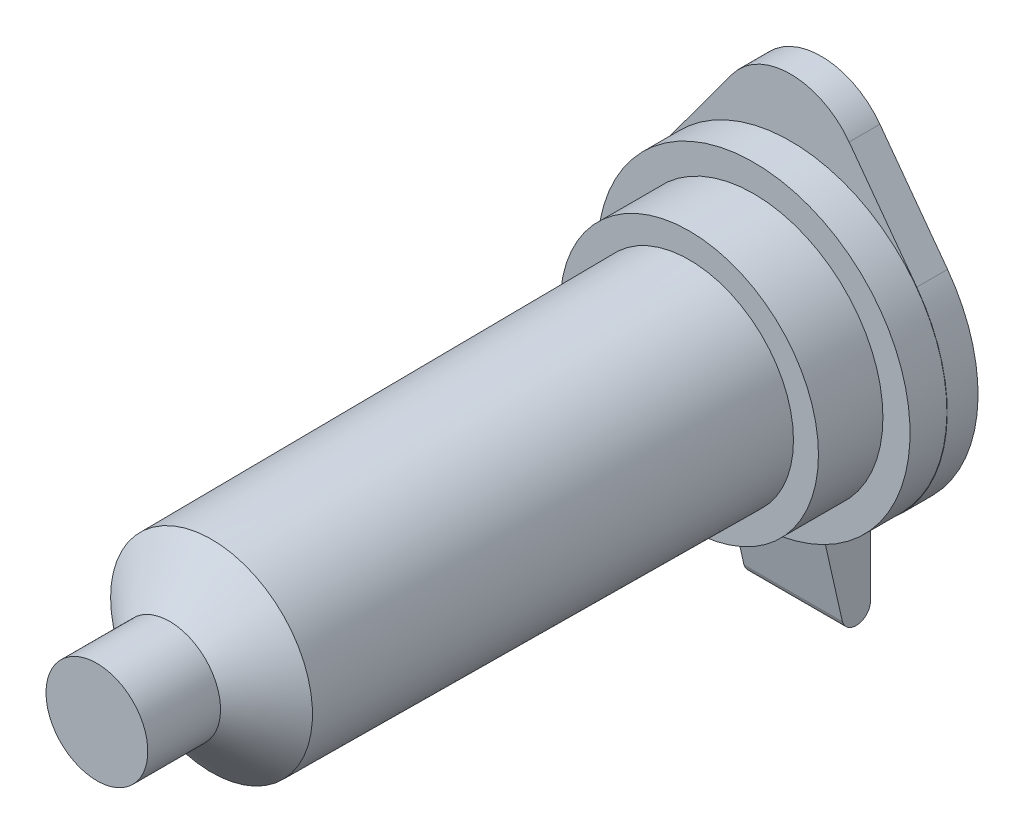
SolidWorks part; units mm, degrees
ref_plane "Front Plane" through (0, 0, 0) normal (0, 0, 1) x (1, 0, 0)
ref_plane "Top Plane" through (0, 0, 0) normal (0, 1, 0) x (1, 0, 0)
ref_plane "Right Plane" through (0, 0, 0) normal (1, 0, 0) x (0, 0, -1)
sketch "Sketch1" plane through (0, 0, 0) normal (0, 1, 0) x (1, 0, 0)
  line L1 (0, 0) -> (2.1, 0)
  line L2 (2.1, 0) -> (2.1, 3)
  line L3 (2.1, 3) -> (4.165, 4.73)
  line L4 (4.165, 4.73) -> (4.3, 24.44)
  line L5 (4.3, 24.44) -> (5.33, 24.44)
  line L6 (5.33, 24.44) -> (5.33, 27.1)
  line L7 (5.33, 27.1) -> (6.45, 27.1)
  line L8 (6.45, 27.1) -> (6.45, 28.62)
  line L9 (6.45, 28.62) -> (0, 28.62)
  line L10 (0, 28.62) -> (0, 0)
  dimension "D1" = 2.1
  dimension "D2" = 3
  dimension "D3" = 4.165
  dimension "D4" = 4.3
  dimension "D5" = 5.33
  dimension "D6" = 6.45
  dimension "D7" = 28.62
  dimension "D8" = 1.52
  dimension "D9" = 4.18
  dimension "D10" = 4.73
revolve "Revolve1" add sketch "Sketch1" angle 360 about L10
sketch "Sketch2" plane through (0, 0, -28.62) normal (0, 0, -1) x (-1, 0, 0)
  line L0 (5.2065, 3.8325) -> (2.416, 7.6234)
  line L1 (-2.416, 7.6234) -> (-5.2065, 3.8325)
  arc A0 (-5.2065, 3.8325) -> (5.2065, 3.8325) centre (0, 0) ccw
  arc A1 (2.416, 7.6234) -> (-2.416, 7.6234) centre (0, 5.845) ccw
  point P5 (0, 8.845)
  point P6 (0, -6.465)
  dimension "D1" = 12.93
  dimension "D3" = 6
  dimension "D2" = 15.31
extrude "Boss-Extrude1" add sketch "Sketch2" along normal blind 1.27
sketch "Sketch3" plane through (0, 0, 0) normal (1, 0, 0) x (0, 0, -1)
  line L0 (29.89, -5.6679) -> (29.89, -9.5931)
  line L1 (29.89, -6.465) -> (29.89, 3.8325) construction
  line L2 (28.7295, -9.7689) -> (27.8039, -5.6679)
  line L3 (27.8039, -5.6679) -> (29.89, -5.6679)
  line L5 (24.44, -5.33) -> (27.1, -5.33) construction
  arc A0 (29.89, -9.5931) -> (28.7295, -9.7689) centre (29.2964, -9.5931) cw
  point P9 (29.3853, -10.18)
  dimension "D1" = 4.85
extrude "Boss-Extrude2" add sketch "Sketch3" along normal mid plane 4.06
